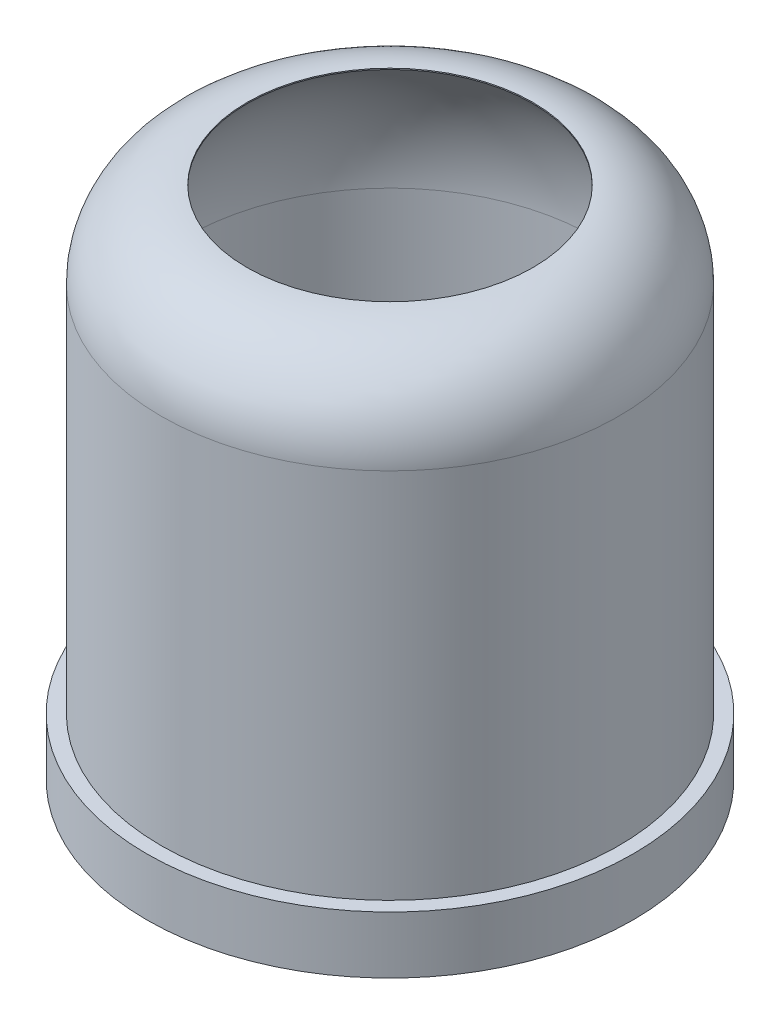
SolidWorks part; units mm, degrees
ref_plane "Front Plane" through (0, 0, 0) normal (0, 0, 1) x (1, 0, 0)
ref_plane "Top Plane" through (0, 0, 0) normal (0, 1, 0) x (1, 0, 0)
ref_plane "Right Plane" through (0, 0, 0) normal (1, 0, 0) x (0, 0, -1)
sketch "Sketch1" plane through (0, 0, 0) normal (0, 0, 1) x (1, 0, 0)
  line L0 (0, 4.5) -> (0, -4.5) construction
  line L1 (-3.125, -4.5) -> (-4.25, -4.5)
  line L2 (-4.25, -4.5) -> (-4.25, -3.5)
  line L3 (-4.25, -3.5) -> (-4, -3.5)
  line L4 (-4, -3.5) -> (-4, 3)
  line L5 (-3.575, 1.925) -> (-3.575, -2.7636)
  line L7 (-2.5, 4.5) -> (-2.5, 4.4805)
  arc A1 (-2.5, 4.4805) -> (-3.575, 1.925) centre (0, 1.925) ccw
  arc A2 (-4, 3) -> (-2.5, 4.5) centre (-2.5, 3) cw
  arc A3 (-3.575, -2.7636) -> (-3.125, -4.5) centre (0, -2.7636) ccw
  dimension "D8" = 7.15
  dimension "D9" = 1.5
  dimension "D1" = 9
  dimension "D2" = 0.25
  dimension "D3" = 4.25
  dimension "D4" = 1
  dimension "D6" = 3.125
  dimension "D7" = 1.7364
  dimension "D10" = 9
  dimension "D11" = 2.5
  dimension "D12" = 0.0195
revolve "Revolve1" add sketch "Sketch1" angle 360 about L0
